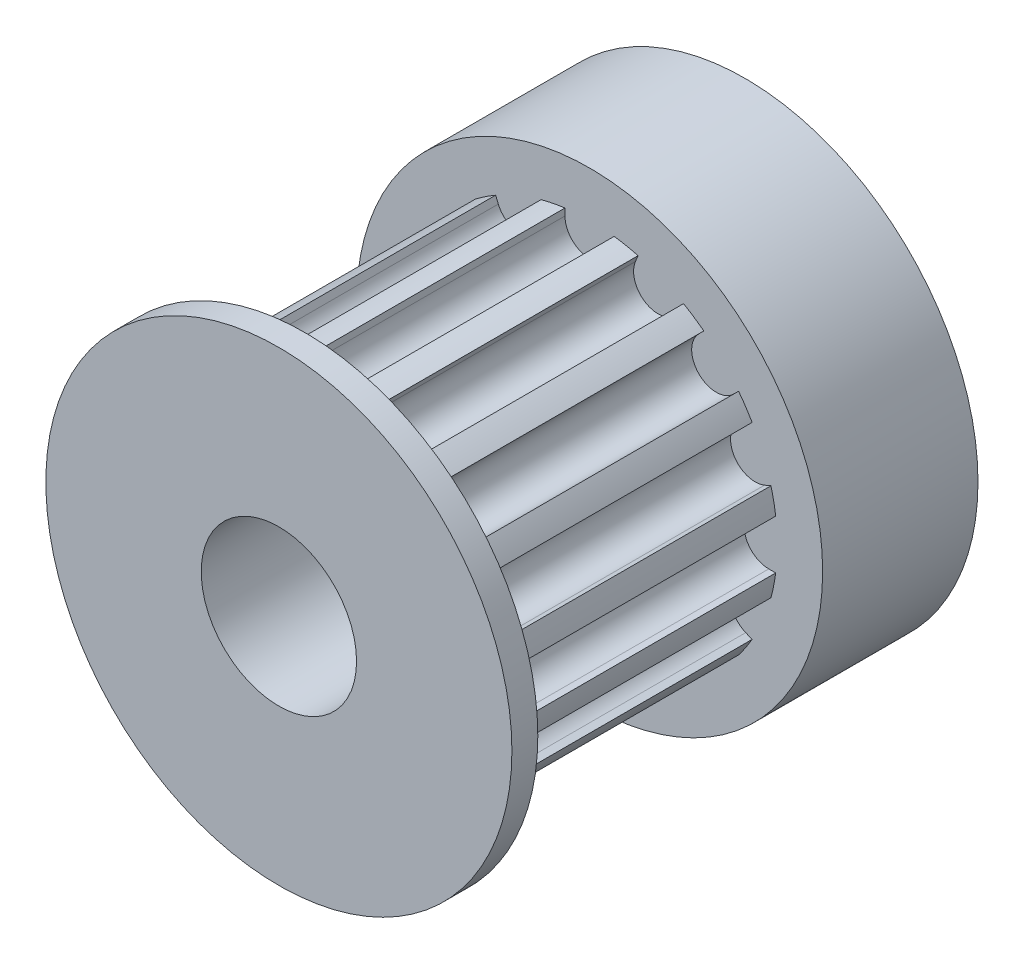
SolidWorks part; units mm, degrees
ref_plane "Front Plane" through (0, 0, 0) normal (0, 0, 1) x (1, 0, 0)
ref_plane "Top Plane" through (0, 0, 0) normal (0, 1, 0) x (1, 0, 0)
ref_plane "Right Plane" through (0, 0, 0) normal (1, 0, 0) x (0, 0, -1)
sketch "Sketch1" plane through (0, 0, 0) normal (0, 0, 1) x (1, 0, 0)
  circle A0 centre (0, 0) radius 3
  circle A1 centre (0, 0) radius 9
  dimension "D1" = 6
  dimension "D2" = 18
extrude "Boss-Extrude1" add sketch "Sketch1" along normal blind 6
sketch "Sketch2" plane through (0, 0, 6) normal (0, 0, 1) x (1, 0, 0)
  circle A0 centre (0, 0) radius 3
  circle A1 centre (0, 0) radius 7.25
  circle A2 centre (0, 0) radius 3 construction
  dimension "D1" = 14.5
extrude "Boss-Extrude2" add sketch "Sketch2" along normal blind 11
sketch "Sketch3" plane through (0, 0, 17) normal (0, 0, 1) x (1, 0, 0)
  circle A0 centre (0, 0) radius 3
  circle A1 centre (0, 0) radius 9
  circle A2 centre (0, 0) radius 3 construction
  dimension "D1" = 18
extrude "Boss-Extrude3" add sketch "Sketch3" along normal blind 1
sketch "Sketch4" plane through (0, 0, 0) normal (0, 1, 0) x (1, 0, 0)
  circle A0 centre (0, -4) radius 1.5
  dimension "D2" = 3
  dimension "D1" = 4
extrude "Cut-Extrude1" cut sketch "Sketch4" against normal through all
sketch "Sketch5" plane through (0, 0, 18) normal (0, 0, 1) x (1, 0, 0)
  line L3 (-0.95, 6.92) -> (-0.95, 7.1875)
  line L4 (0.95, 6.92) -> (0.95, 7.1875)
  line L5 (0, 6.92) -> (0, 7.25) construction
  line L6 (1.7705, 6.7568) -> (1.8728, 7.0039)
  line L7 (3.5259, 6.0297) -> (3.6282, 6.2768)
  line L8 (4.2214, 5.5649) -> (4.4106, 5.7541)
  line L9 (5.5649, 4.2214) -> (5.7541, 4.4106)
  line L10 (6.0297, 3.5259) -> (6.2768, 3.6282)
  line L11 (6.7568, 1.7705) -> (7.0039, 1.8728)
  line L12 (6.92, 0.95) -> (7.1875, 0.95)
  line L13 (6.92, -0.95) -> (7.1875, -0.95)
  line L14 (6.7568, -1.7705) -> (7.0039, -1.8728)
  line L15 (6.0297, -3.5259) -> (6.2768, -3.6282)
  line L16 (5.5649, -4.2214) -> (5.7541, -4.4106)
  line L17 (4.2214, -5.5649) -> (4.4106, -5.7541)
  line L18 (3.5259, -6.0297) -> (3.6282, -6.2768)
  line L19 (1.7705, -6.7568) -> (1.8728, -7.0039)
  line L20 (0.95, -6.92) -> (0.95, -7.1875)
  line L21 (-0.95, -6.92) -> (-0.95, -7.1875)
  line L22 (-1.7705, -6.7568) -> (-1.8728, -7.0039)
  line L23 (-3.5259, -6.0297) -> (-3.6282, -6.2768)
  line L24 (-4.2214, -5.5649) -> (-4.4106, -5.7541)
  line L25 (-5.5649, -4.2214) -> (-5.7541, -4.4106)
  line L26 (-6.0297, -3.5259) -> (-6.2768, -3.6282)
  line L27 (-6.7568, -1.7705) -> (-7.0039, -1.8728)
  line L28 (-6.92, -0.95) -> (-7.1875, -0.95)
  line L29 (-6.92, 0.95) -> (-7.1875, 0.95)
  line L30 (-6.7568, 1.7705) -> (-7.0039, 1.8728)
  line L31 (-6.0297, 3.5259) -> (-6.2768, 3.6282)
  line L32 (-5.5649, 4.2214) -> (-5.7541, 4.4106)
  line L33 (-4.2214, 5.5649) -> (-4.4106, 5.7541)
  line L34 (-3.5259, 6.0297) -> (-3.6282, 6.2768)
  line L35 (-1.7705, 6.7568) -> (-1.8728, 7.0039)
  circle A0 centre (0, 0) radius 7.25 construction
  arc A2 (-0.95, 6.92) -> (0.95, 6.92) centre (0, 6.92) ccw
  arc A4 (1.7705, 6.7568) -> (3.5259, 6.0297) centre (2.6482, 6.3932) ccw
  arc A6 (4.2214, 5.5649) -> (5.5649, 4.2214) centre (4.8932, 4.8932) ccw
  arc A8 (6.0297, 3.5259) -> (6.7568, 1.7705) centre (6.3932, 2.6482) ccw
  arc A10 (6.92, 0.95) -> (6.92, -0.95) centre (6.92, 0) ccw
  arc A12 (6.7568, -1.7705) -> (6.0297, -3.5259) centre (6.3932, -2.6482) ccw
  arc A14 (5.5649, -4.2214) -> (4.2214, -5.5649) centre (4.8932, -4.8932) ccw
  arc A16 (3.5259, -6.0297) -> (1.7705, -6.7568) centre (2.6482, -6.3932) ccw
  arc A18 (0.95, -6.92) -> (-0.95, -6.92) centre (0, -6.92) ccw
  arc A20 (-1.7705, -6.7568) -> (-3.5259, -6.0297) centre (-2.6482, -6.3932) ccw
  arc A22 (-4.2214, -5.5649) -> (-5.5649, -4.2214) centre (-4.8932, -4.8932) ccw
  arc A24 (-6.0297, -3.5259) -> (-6.7568, -1.7705) centre (-6.3932, -2.6482) ccw
  arc A26 (-6.92, -0.95) -> (-6.92, 0.95) centre (-6.92, 0) ccw
  arc A28 (-6.7568, 1.7705) -> (-6.0297, 3.5259) centre (-6.3932, 2.6482) ccw
  arc A30 (-5.5649, 4.2214) -> (-4.2214, 5.5649) centre (-4.8932, 4.8932) ccw
  arc A32 (-3.5259, 6.0297) -> (-1.7705, 6.7568) centre (-2.6482, 6.3932) ccw
  arc A35 (-1.8728, 7.0039) -> (-0.95, 7.1875) centre (0, 0) cw
  arc A36 (0.95, 7.1875) -> (1.8728, 7.0039) centre (0, 0) cw
  arc A37 (3.6282, 6.2768) -> (4.4106, 5.7541) centre (0, 0) cw
  arc A40 (5.7541, 4.4106) -> (6.2768, 3.6282) centre (0, 0) cw
  arc A41 (7.0039, 1.8728) -> (7.1875, 0.95) centre (0, 0) cw
  arc A42 (7.1875, -0.95) -> (7.0039, -1.8728) centre (0, 0) cw
  arc A43 (5.7541, -4.4106) -> (6.2768, -3.6282) centre (0, 0) ccw
  arc A44 (3.6282, -6.2768) -> (4.4106, -5.7541) centre (0, 0) ccw
  arc A45 (1.8728, -7.0039) -> (0.95, -7.1875) centre (0, 0) cw
  arc A46 (-0.95, -7.1875) -> (-1.8728, -7.0039) centre (0, 0) cw
  arc A47 (-3.6282, -6.2768) -> (-4.4106, -5.7541) centre (0, 0) cw
  arc A48 (-5.7541, -4.4106) -> (-6.2768, -3.6282) centre (0, 0) cw
  arc A49 (-7.0039, -1.8728) -> (-7.1875, -0.95) centre (0, 0) cw
  arc A50 (-7.1875, 0.95) -> (-7.0039, 1.8728) centre (0, 0) cw
  arc A51 (-6.2768, 3.6282) -> (-5.7541, 4.4106) centre (0, 0) cw
  arc A52 (-4.4106, 5.7541) -> (-3.6282, 6.2768) centre (0, 0) cw
  point P6 (0, 5.97)
  dimension "D1" = 14.5
  dimension "D2" = 0.95
  dimension "D3" = 16
  dimension "D4" = 1.28
extrude "Cut-Extrude4" cut sketch "Sketch5" against normal blind 11 from offset 1
